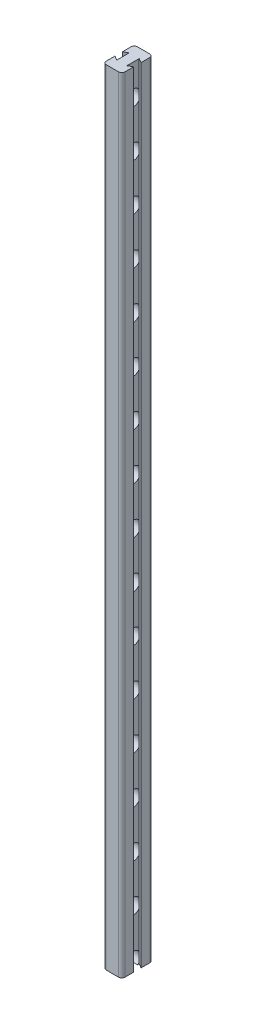
SolidWorks part; units mm, degrees
material "5052-H32"
ref_plane "Front Plane" through (0, 0, 0) normal (0, 0, 1) x (1, 0, 0)
ref_plane "Top Plane" through (0, 0, 0) normal (0, 1, 0) x (1, 0, 0)
ref_plane "Right Plane" through (0, 0, 0) normal (1, 0, 0) x (0, 0, -1)
sketch "Sketch1" plane through (0, 0, 0) normal (0, 1, 0) x (1, 0, 0)
  line L5 (15, 25) -> (15, 5.9585)
  line L6 (15, 5.9585) -> (8, 10)
  line L7 (8, 10) -> (8, -10)
  line L8 (8, -10) -> (15, -5.9585)
  line L9 (15, -5.9585) -> (15, -25)
  line L16 (-15, -25) -> (-15, -5.9585)
  line L17 (-15, -5.9585) -> (-8, -10)
  line L18 (-8, -10) -> (-8, 10)
  line L19 (-8, 10) -> (-15, 5.9585)
  line L20 (-15, 5.9585) -> (-15, 25)
  line L21 (0, 36.7762) -> (0, -31.0073) construction
  line L22 (-32.2836, 0) -> (31.3226, 0) construction
  line L23 (-15, 25) -> (15, 25)
  line L24 (-15, -25) -> (15, -25)
  point P2 (0, 25)
  point P30 (-8, 0)
  point P43 (8, 0)
  dimension "D5" = 7
  dimension "D6" = 7
  dimension "D7" = 20
  dimension "D8" = 60
  dimension "D10" = 60
  dimension "D11" = 30
  dimension "D12" = 60
  dimension "D13" = 60
extrude "Boss-Extrude1" add sketch "Sketch1" along normal blind 1260
sketch "Sketch3" plane through (0, 0, 0) normal (1, 0, 0) x (0, 0, -1)
  line L0 (-10, 1260) -> (10, 1260) construction
  line L2 (0, 1796.6199) -> (0, -77.2619) construction
  line L3 (25, 1260) -> (25, 0) construction
  circle A0 centre (0, 1210) radius 12.5
  circle A1 centre (0, 1135) radius 12.5
  circle A2 centre (0, 1060) radius 12.5
  circle A3 centre (0, 985) radius 12.5
  circle A4 centre (0, 910) radius 12.5
  circle A5 centre (0, 835) radius 12.5
  circle A6 centre (0, 760) radius 12.5
  circle A7 centre (0, 685) radius 12.5
  circle A8 centre (0, 610) radius 12.5
  circle A9 centre (0, 535) radius 12.5
  circle A10 centre (0, 460) radius 12.5
  circle A11 centre (0, 385) radius 12.5
  circle A12 centre (0, 310) radius 12.5
  circle A13 centre (0, 235) radius 12.5
  circle A14 centre (0, 160) radius 12.5
  circle A15 centre (0, 85) radius 12.5
  circle A16 centre (0, 10) radius 12.5
  circle A23 centre (0, -65) radius 12.5 [skipped]
  circle A24 centre (0, -140) radius 12.5 [skipped]
  circle A25 centre (0, -215) radius 12.5 [skipped]
  circle A26 centre (0, -290) radius 12.5 [skipped]
  circle A27 centre (0, -365) radius 12.5 [skipped]
  circle A28 centre (0, -440) radius 12.5 [skipped]
  dimension "D1" = 25
  dimension "D2" = 50
  dimension "D3" = 25
  dimension "D4" = 23
extrude "Cut-Extrude1" cut sketch "Sketch3" against normal blind 8 and the other way blind 8
fillet "Fillet1" radius 5 4 edges at (-15, 630, 25) (15, 630, 25) (15, 630, -25) (-15, 630, -25)
